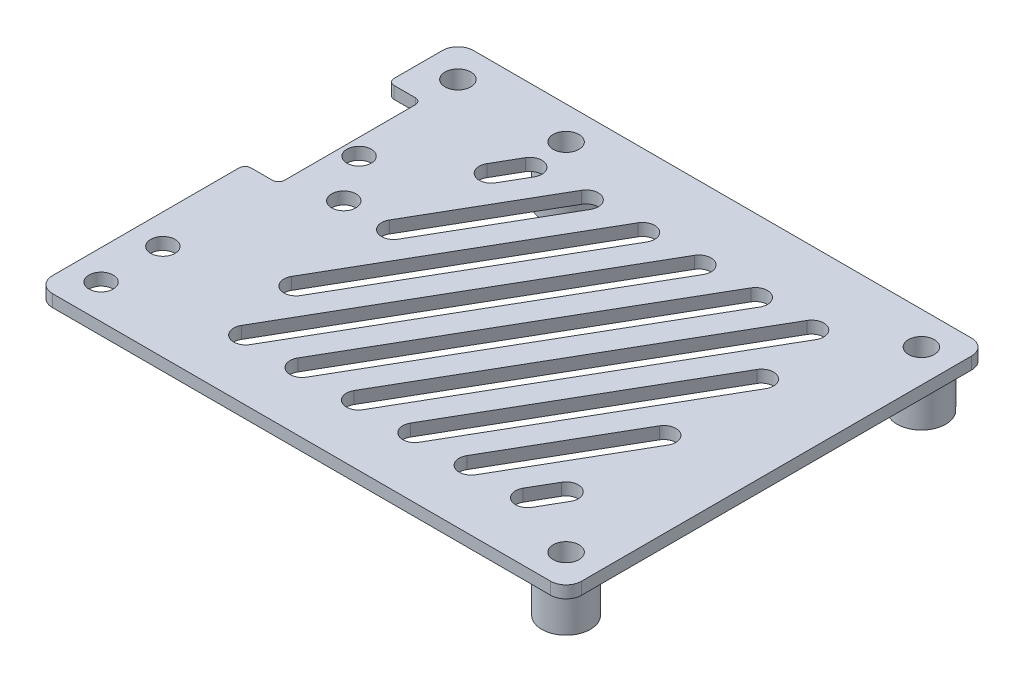
SolidWorks part; units mm, degrees
ref_plane "Front Plane" through (0, 0, 0) normal (0, 0, 1) x (1, 0, 0)
ref_plane "Top Plane" through (0, 0, 0) normal (0, 1, 0) x (1, 0, 0)
ref_plane "Right Plane" through (0, 0, 0) normal (1, 0, 0) x (0, 0, -1)
sketch "Sketch1" plane through (0, 0, 0) normal (0, 1, 0) x (1, 0, 0)
  line L0 (38.1, -29.21) -> (43.5, -34.61)
  line L1 (-38.1, -29.21) -> (38.1, -29.21) construction
  line L2 (-38.1, -29.21) -> (-38.1, 29.21) construction
  line L3 (-38.1, 29.21) -> (38.1, 29.21) construction
  line L4 (38.1, -29.21) -> (38.1, 29.21) construction
  line L5 (-38.1, -29.21) -> (38.1, 29.21) construction
  line L6 (-38.1, 29.21) -> (38.1, -29.21) construction
  line L7 (-43.5, -34.61) -> (43.5, -34.61)
  line L8 (-43.5, -34.61) -> (-43.5, 34.61)
  line L9 (-43.5, 34.61) -> (43.5, 34.61)
  line L10 (43.5, -34.61) -> (43.5, 34.61)
  line L11 (-43.5, -34.61) -> (43.5, 34.61) construction
  line L12 (-43.5, 34.61) -> (43.5, -34.61) construction
  circle A0 centre (-38.1, 29.21) radius 2.125
  circle A1 centre (38.1, 29.21) radius 2.125
  circle A2 centre (-20.32, 29.21) radius 2.125
  circle A3 centre (38.1, -29.21) radius 2.125
  point P0 (0, 0)
  point P11 (0, 0)
  dimension "D3" = 4.25
  dimension "D1" = 58.42
  dimension "D2" = 76.2
  dimension "D4" = 17.78
  dimension "D5" = 87
  dimension "D6" = 45
extrude "Boss-Extrude1" add sketch "Sketch1" along normal blind 2
sketch "Sketch2" plane through (0, 0, 0) normal (0, -1, 0) x (1, 0, 0)
  circle A0 centre (38.1, -29.21) radius 4
  circle A1 centre (38.1, -29.21) radius 2.125
  circle A2 centre (38.1, -29.21) radius 2.125
  circle A3 centre (-38.1, -29.21) radius 2.125
  circle A4 centre (-38.1, -29.21) radius 2.125
  circle A5 centre (-20.32, -29.21) radius 2.125
  circle A6 centre (-20.32, -29.21) radius 2.125
  circle A7 centre (38.1, 29.21) radius 2.125
  circle A8 centre (38.1, 29.21) radius 2.125
  circle A9 centre (-20.32, -29.21) radius 4
  circle A10 centre (-38.1, -29.21) radius 4
  circle A11 centre (38.1, 29.21) radius 4
  dimension "D5" = 8
  dimension "D1" = 0
  dimension "D2" = 0
  dimension "D3" = 0
  dimension "D4" = 0
extrude "Boss-Extrude2" add sketch "Sketch2" along normal blind 7
sketch "Sketch3" plane through (0, 2, 0) normal (0, 1, 0) x (1, 0, 0)
  line L0 (-43.5, -34.61) -> (-43.5, 34.61) construction
  line L1 (-43.5, 23.11) -> (-38, 23.11)
  line L2 (-43.5, 23.11) -> (-43.5, -0.39)
  line L3 (-43.5, -0.39) -> (-38, -0.39)
  line L4 (-38, 23.11) -> (-38, -0.39)
  line L5 (-43.5, 34.61) -> (43.5, 34.61) construction
  line L6 (43.5, -34.61) -> (43.5, 34.61) construction
  line L7 (43.5, -21.11) -> (38, -21.11)
  line L8 (43.5, -21.11) -> (43.5, -12.61)
  line L9 (43.5, -12.61) -> (38, -12.61)
  line L10 (38, -21.11) -> (38, -12.61)
  line L11 (-43.5, -34.61) -> (43.5, -34.61) construction
  circle A0 centre (38.1, -29.21) radius 2.125 construction
  circle A1 centre (38.1, -29.21) radius 2.125
  line M5 (-43.5, 34.61) -> (-43.5, -34.61)
  dimension "D1" = 11.5
  dimension "D2" = 5.5
  dimension "D3" = 23.5
  dimension "D4" = 5.5
  dimension "D5" = 13.5
  dimension "D6" = 8.5
extrude "Cut-Extrude1" cut sketch "Sketch3" against normal blind 7 contours L4 L1 L3 M5
sketch "Sketch4" plane through (0, 2, 0) normal (0, 1, 0) x (1, 0, 0)
  line L1 (-43.5, -34.61) -> (43.5, -34.61) construction
  line L2 (-38, -0.39) -> (-38, 23.11) construction
  line L3 (-38, 23.11) -> (-43.5, 23.11) construction
  line L4 (-43.5, -34.61) -> (-43.5, -0.39) construction
  circle A0 centre (-38.59, -28.97) radius 2
  circle A1 centre (-38.59, -18.81) radius 2
  circle A2 centre (-35.3, 10.16) radius 2
  dimension "D1" = 4
  dimension "D2" = 4.91
  dimension "D3" = 5.64
  dimension "D4" = 10.16
  dimension "D5" = 2.7
  dimension "D6" = 12.95
extrude "Cut-Extrude2" cut sketch "Sketch4" against normal blind 7
sketch "Sketch5" plane through (0, 2, 0) normal (0, 1, 0) x (1, 0, 0)
  line L0 (-22, 18.61) -> (-19.6906, 22.61) construction
  line L1 (-23.7321, 19.61) -> (-21.4226, 23.61)
  line L2 (-20.2679, 17.61) -> (-17.9585, 21.61)
  line L3 (-43.5, 34.61) -> (43.5, 34.61) construction
  line L4 (-22, 22.61) -> (29.5, 22.61) construction
  line L5 (-22, 22.61) -> (-22, -24.61) construction
  line L6 (-22, -24.61) -> (29.5, -24.61) construction
  line L7 (29.5, 22.61) -> (29.5, -24.61) construction
  line L8 (-43.5, -34.61) -> (43.5, -34.61) construction
  line L10 (-38, -0.39) -> (-38, 23.11) construction
  line L11 (-22, 2.5574) -> (-10.4226, 22.61) construction
  line L12 (-23.7321, 3.5574) -> (-12.1547, 23.61)
  line L13 (-20.2679, 1.5574) -> (-8.6906, 21.61)
  line L14 (-22, -13.4952) -> (-1.1547, 22.61) construction
  line L15 (-23.7321, -12.4952) -> (-2.8867, 23.61)
  line L16 (-20.2679, -14.4952) -> (0.5774, 21.61)
  line L17 (8.1133, 22.61) -> (-19.1492, -24.61) construction
  line L18 (9.8453, 21.61) -> (-17.4171, -25.61)
  line L19 (6.3812, 23.61) -> (-20.8813, -23.61)
  line L20 (-9.8812, -24.61) -> (17.3812, 22.61) construction
  line L21 (-11.6133, -23.61) -> (15.6492, 23.61)
  line L22 (-8.1492, -25.61) -> (19.1133, 21.61)
  line L23 (26.6492, 22.61) -> (-0.6133, -24.61) construction
  line L24 (28.3813, 21.61) -> (1.1188, -25.61)
  line L25 (24.9171, 23.61) -> (-2.3453, -23.61)
  line L26 (8.6547, -24.61) -> (29.5, 11.4952) construction
  line L27 (6.9226, -23.61) -> (27.7679, 12.4952)
  line L28 (10.3867, -25.61) -> (31.2321, 10.4952)
  line L29 (29.5, -4.5574) -> (17.9226, -24.61) construction
  line L30 (31.2321, -5.5574) -> (19.6547, -25.61)
  line L31 (27.7679, -3.5574) -> (16.1906, -23.61)
  line L32 (27.1906, -24.61) -> (29.5, -20.61) construction
  line L33 (25.4585, -23.61) -> (27.7679, -19.61)
  line L34 (28.9226, -25.61) -> (31.2321, -21.61)
  line L38 (-19.1132, 19.61) -> (-15.6264, 17.5969) construction
  line L39 (-14.4793, 11.5837) -> (-10.9924, 9.5706) construction
  line L40 (-9.8453, 3.5574) -> (-6.3584, 1.5443) construction
  line L41 (-3.7859, -2) -> (-0.299, -4.0131) construction
  line L42 (5.4821, -2) -> (8.9689, -4.0131) construction
  line L43 (14.75, -2) -> (18.2369, -4.0131) construction
  line L44 (20.8094, -7.5574) -> (24.2963, -9.5706) construction
  line L45 (25.4434, -15.5837) -> (28.9302, -17.5969) construction
  line L47 (43.5, -34.61) -> (43.5, 34.61) construction
  arc A0 (-23.7321, 19.61) -> (-20.2679, 17.61) centre (-22, 18.61) ccw
  arc A1 (-17.9585, 21.61) -> (-21.4226, 23.61) centre (-19.6906, 22.61) ccw
  arc A2 (-23.7321, 3.5574) -> (-20.2679, 1.5574) centre (-22, 2.5574) ccw
  arc A3 (-8.6906, 21.61) -> (-12.1547, 23.61) centre (-10.4226, 22.61) ccw
  arc A4 (-23.7321, -12.4952) -> (-20.2679, -14.4952) centre (-22, -13.4952) ccw
  arc A5 (0.5774, 21.61) -> (-2.8867, 23.61) centre (-1.1547, 22.61) ccw
  arc A6 (9.8453, 21.61) -> (6.3812, 23.61) centre (8.1133, 22.61) ccw
  arc A7 (-20.8813, -23.61) -> (-17.4171, -25.61) centre (-19.1492, -24.61) ccw
  arc A8 (-11.6133, -23.61) -> (-8.1492, -25.61) centre (-9.8812, -24.61) ccw
  arc A9 (19.1133, 21.61) -> (15.6492, 23.61) centre (17.3812, 22.61) ccw
  arc A10 (28.3813, 21.61) -> (24.9171, 23.61) centre (26.6492, 22.61) ccw
  arc A11 (-2.3453, -23.61) -> (1.1188, -25.61) centre (-0.6133, -24.61) ccw
  arc A12 (6.9226, -23.61) -> (10.3867, -25.61) centre (8.6547, -24.61) ccw
  arc A13 (31.2321, 10.4952) -> (27.7679, 12.4952) centre (29.5, 11.4952) ccw
  arc A14 (31.2321, -5.5574) -> (27.7679, -3.5574) centre (29.5, -4.5574) ccw
  arc A15 (16.1906, -23.61) -> (19.6547, -25.61) centre (17.9226, -24.61) ccw
  arc A16 (25.4585, -23.61) -> (28.9226, -25.61) centre (27.1906, -24.61) ccw
  arc A17 (31.2321, -21.61) -> (27.7679, -19.61) centre (29.5, -20.61) ccw
  point P2 (-20.8453, 20.61)
  point P11 (-16.2113, 12.5837)
  point P28 (-11.5773, 4.5574)
  point P35 (-5.518, -1)
  point P40 (3.75, -1)
  point P47 (13.018, -1)
  point P56 (19.0773, -6.5574)
  point P61 (23.7113, -14.5837)
  point P68 (28.3453, -22.61)
  dimension "D1" = 2
  dimension "D2" = 60
  dimension "D3" = 12
  dimension "D4" = 10
  dimension "D5" = 14
  dimension "D6" = 16
extrude "Cut-Extrude3" cut sketch "Sketch5" against normal blind 5
sketch "Sketch6" plane through (0, 2, 0) normal (0, 1, 0) x (1, 0, 0)
  line L1 (-43.5, -34.61) -> (43.5, -34.61) construction
  line L2 (-43.5, -34.61) -> (-43.5, -0.39) construction
  circle A0 centre (-30.2, 2.54) radius 2
  dimension "D1" = 4
  dimension "D2" = 13.3
  dimension "D3" = 37.15
extrude "Cut-Extrude4" cut sketch "Sketch6" against normal blind 10
fillet "Fillet1" radius 1 4 edges at (-38, 1, 0.39) (-43.5, 1, 0.39) (-38, 1, -23.11) (-43.5, 1, -23.11)
fillet "Fillet2" radius 2.54 4 edges at (43.5, 1, -34.61) (43.5, 1, 34.61) (-43.5, 1, 34.61) (-43.5, 1, -34.61)
